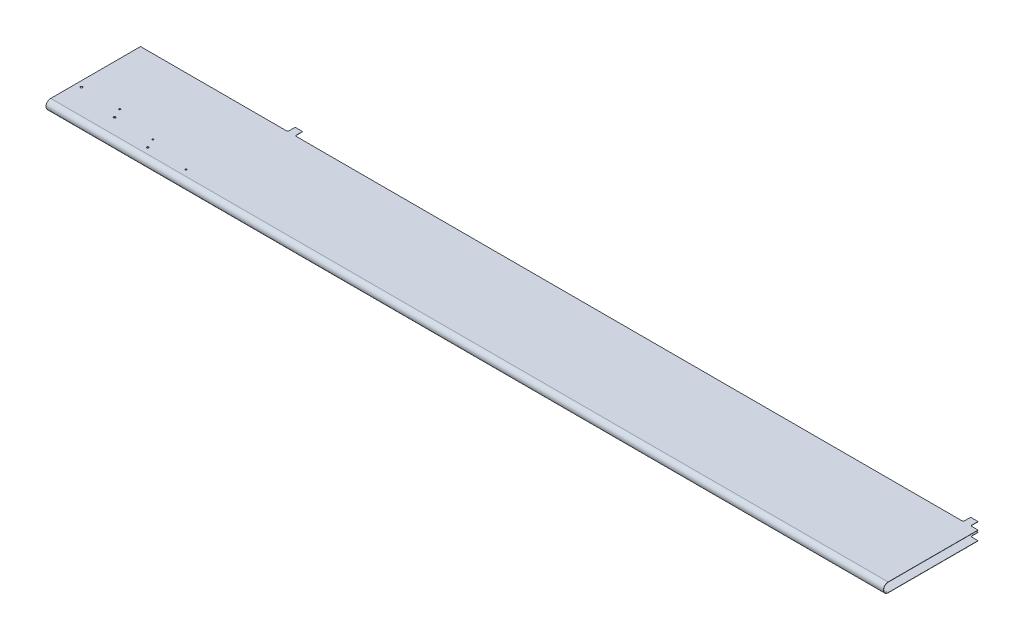
SolidWorks part; units mm, degrees
material "Kapton"
ref_plane "Front Plane" through (0, 0, 0) normal (0, 0, 1) x (1, 0, 0)
ref_plane "Top Plane" through (0, 0, 0) normal (0, 1, 0) x (1, 0, 0)
ref_plane "Right Plane" through (0, 0, 0) normal (1, 0, 0) x (0, 0, -1)
sketch "Sketch1" plane through (0, 0, 0) normal (1, 0, 0) x (0, 0, -1)
  line L0 (0, 0) -> (-61, 0)
  line L1 (-61, -6.4251) -> (0, -6.4251)
  line L2 (0, 0) -> (5, 0)
  line L3 (0, -6.4251) -> (5, -6.4251)
  line L4 (0, 0) -> (0, -6.4251) construction
  line L5 (5, -0.1626) -> (-61, -0.1626)
  line L6 (5, -6.2626) -> (-61, -6.2626)
  line L9 (5, 0) -> (5, -6.4251) construction
  line L10 (5, 0) -> (5, -0.1626)
  line L11 (5, -6.2626) -> (5, -6.4251)
  arc A0 (-61, 0) -> (-61, -6.4251) centre (-61, -3.2126) ccw
  arc A1 (-61, -0.1626) -> (-61, -6.2626) centre (-61, -3.2126) ccw
  point P5 (0, -0.1626)
  point P10 (-60.9777, -0.1626)
  point P12 (-60.9777, -6.2626)
  point P13 (0, -6.2626)
  dimension "D4" = 0.1626
  dimension "D6" = 0.1626
  dimension "D7" = 3.2126
  dimension "D8" = 0.1626
  dimension "D2" = 61
  dimension "D3" = 5
  dimension "D5" = 61
  dimension "D1" = 6.1
extrude "Boss-Extrude1" add sketch "Sketch1" against normal blind 563.8 and the other way blind 5
sketch "Sketch2" plane through (0, 0, 0) normal (0, 1, 0) x (1, 0, 0)
  line L0 (5, 0) -> (1, 0)
  line L1 (5, 5) -> (5, -61) construction
  line L2 (0, 1) -> (0, 5)
  line L3 (-563.8, 5) -> (5, 5) construction
  line L4 (0, 5) -> (-5, 5)
  line L5 (-5, 5) -> (-5, 1)
  line L6 (-6, 0) -> (-457.8, 0)
  line L7 (-458.8, 1) -> (-458.8, 5)
  line L8 (-458.8, 5) -> (-463.8, 5)
  line L9 (-463.8, 5) -> (-463.8, 1)
  line L10 (-464.8, 0) -> (-563.8, 0)
  line L11 (-563.8, 5) -> (-563.8, -61) construction
  line L12 (-563.8, 0) -> (-563.8, 10)
  line L13 (-563.8, 10) -> (5, 10)
  line L14 (5, 10) -> (5, 0)
  arc A0 (-464.8, 0) -> (-463.8, 1) centre (-464.8, 1) ccw
  arc A1 (-457.8, 0) -> (-458.8, 1) centre (-457.8, 1) cw
  arc A2 (-6, 0) -> (-5, 1) centre (-6, 1) ccw
  arc A3 (0, 1) -> (1, 0) centre (1, 1) ccw
  point P22 (-458.8, 0)
  point P25 (-5, 0)
  point P28 (0, 0)
  dimension "D7" = 1
  dimension "D1" = 5
  dimension "D2" = 5
  dimension "D3" = 10
  dimension "D4" = 453.8
  dimension "D5" = 5
  dimension "D6" = 5
extrude "Cut-Extrude1" cut sketch "Sketch2" against normal through all
sketch "Sketch3" plane through (-563.8, 0, 0) normal (-1, 0, 0) x (0, 0, 1)
  line L2 (61, -0.2311) -> (0, -0.2311)
  line L3 (0, -6.194) -> (61, -6.194)
  line L4 (0, -0.2311) -> (0, 0)
  line L5 (0, 0) -> (61, 0)
  line L6 (61, -6.4251) -> (0, -6.4251)
  line L7 (0, -6.4251) -> (0, -6.194)
  line L8 (61, -0.2311) -> (61, 0) construction
  line L9 (61, -6.194) -> (61, -6.4251) construction
  line L10 (0, 0) -> (61, 0) construction
  line L11 (61, -6.4251) -> (0, -6.4251) construction
  arc A0 (61, -6.4251) -> (61, 0) centre (61, -3.2126) ccw construction
  arc A1 (61, -0.2311) -> (61, -6.194) centre (61, -3.2126) cw
  arc A2 (61, 0) -> (61, -6.4251) centre (61, -3.2126) cw
  arc A5 (61, -0.2311) -> (61, -6.194) centre (61, -3.2126) cw construction
  dimension "D3" = 0.2311
  dimension "D1" = 0.2311
  dimension "D2" = 0.2311
extrude "Boss-Extrude2" add sketch "Sketch3" against normal blind 91.3
sketch "Sketch4" plane through (0, 0, 0) normal (0, 1, 0) x (1, 0, 0)
  line L0 (-560.001, -43.918) -> (-563.8, -43.918) construction
  line L1 (-563.8, 0) -> (-563.8, -61) construction
  line L2 (-560.001, -43.918) -> (-534.001, -43.918) construction
  line L6 (-531.001, -50.418) -> (-531.001, -56.918) construction
  line L7 (-531.001, -56.918) -> (-502.001, -56.918) construction
  line L8 (-531.001, -50.418) -> (-505.001, -50.418) construction
  line L10 (-502.001, -56.918) -> (-476.001, -56.918) construction
  line L11 (-560.001, -43.918) -> (-560.001, 0) construction
  line L12 (-563.8, 0) -> (-464.8, 0) construction
  line L13 (-560.001, -43.918) -> (-560.001, -50.418) construction
  line L14 (-560.001, -50.418) -> (-531.001, -50.418) construction
  circle A0 centre (-560.001, -43.918) radius 0.69
  circle A1 centre (-534.001, -43.918) radius 0.51
  circle A2 centre (-531.001, -50.418) radius 0.69
  circle A3 centre (-505.001, -50.418) radius 0.51
  circle A4 centre (-502.001, -56.918) radius 0.69
  circle A5 centre (-476.001, -56.918) radius 0.51
  dimension "D10" = 1.38
  dimension "D11" = 1.02
  dimension "D1" = 3.799
  dimension "D2" = 26
  dimension "D3" = 29
  dimension "D4" = 26
  dimension "D5" = 29
  dimension "D6" = 26
  dimension "D7" = 43.918
  dimension "D8" = 6.5
  dimension "D9" = 6.5
extrude "Cut-Extrude2" cut sketch "Sketch4" against normal blind 2
